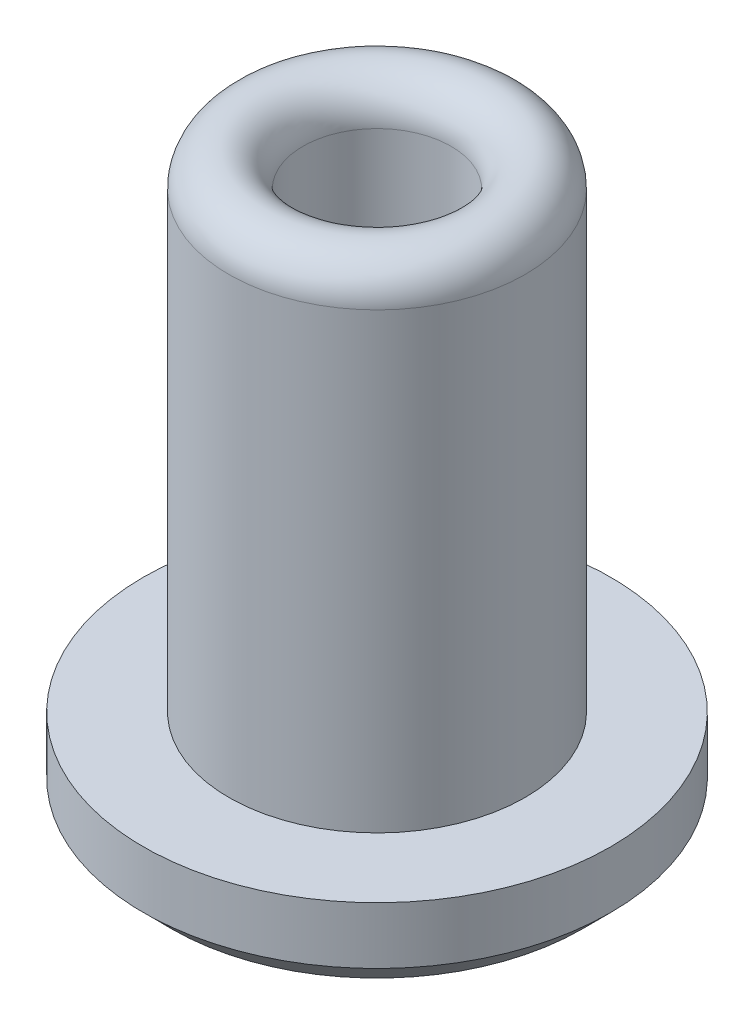
SolidWorks part; units mm, degrees
material "ABS PC"
ref_plane "Front Plane" through (0, 0, 0) normal (0, 0, 1) x (1, 0, 0)
ref_plane "Top Plane" through (0, 0, 0) normal (0, 1, 0) x (1, 0, 0)
ref_plane "Right Plane" through (0, 0, 0) normal (1, 0, 0) x (0, 0, -1)
sketch "Sketch1" plane through (0, 0, 0) normal (0, 0, 1) x (1, 0, 0)
  line L0 (0, -1000) -> (0, 49000) construction
  line L1 (0, 0) -> (0, 0.5)
  line L3 (-2.6, 9.45) -> (-2.6, 1.5)
  line L4 (-2.6, 1.5) -> (-4.1, 1.5)
  line L5 (-4.1, 1.5) -> (-4.1, 0)
  line L6 (-4.1, 0) -> (0, 0)
  line L7 (-1.3, 9.45) -> (-1.3, 1.5)
  line L8 (-0.3, 0.5) -> (0, 0.5)
  arc A0 (-1.3, 1.5) -> (-0.3, 0.5) centre (-0.3, 1.5) ccw
  arc A1 (-2.6, 9.45) -> (-1.3, 9.45) centre (-1.95, 9.45) cw
  point P14 (-1.95, 10.1)
  dimension "D6" = 1
  dimension "D1" = 5.2
  dimension "D2" = 8.6
  dimension "D3" = 1.5
  dimension "D4" = 1.5
  dimension "D5" = 0.5
  dimension "D7" = 2.6
revolve "Revolve1" add sketch "Sketch1" angle 360 about L0
chamfer "Chamfer1" distance 0.5 angle 45 1 edges at (4.1, 0, 0)
